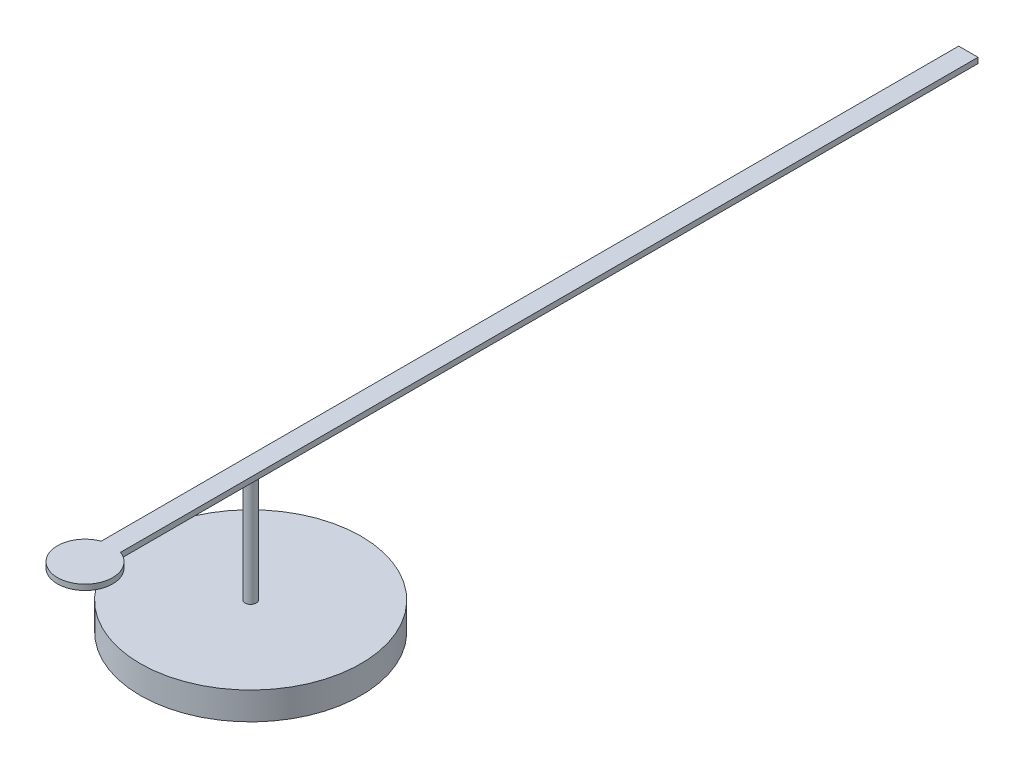
SolidWorks part; units mm, degrees
ref_plane "Front Plane" through (0, 0, 0) normal (0, 0, 1) x (1, 0, 0)
ref_plane "Top Plane" through (0, 0, 0) normal (0, 1, 0) x (1, 0, 0)
ref_plane "Right Plane" through (0, 0, 0) normal (1, 0, 0) x (0, 0, -1)
sketch "Sketch1" plane through (0, 0, 0) normal (0, 1, 0) x (1, 0, 0)
  line L0 (0, 71.7393) -> (0, -94.0328) construction
  line L1 (-2.0666, 0) -> (2.0487, 0) construction
  line L2 (-0.175, 0.4684) -> (-0.175, 13)
  line L4 (-0.175, -2.5316) -> (-0.175, -0.4684)
  line L5 (-0.175, 13) -> (0.175, 13)
  line L6 (0.175, -2.5316) -> (0.175, -0.4684)
  line L7 (0.175, 0.4684) -> (0.175, 13)
  line L8 (0.175, 0.4684) -> (0.175, -0.4684)
  line L9 (-0.175, 0.4684) -> (-0.175, -0.4684)
  arc A0 (0.175, -0.4684) -> (0.175, 0.4684) centre (0, 0) ccw construction
  arc A1 (-0.175, 0.4684) -> (-0.175, -0.4684) centre (0, 0) ccw construction
  arc A2 (-0.175, -2.5316) -> (0.175, -2.5316) centre (0, -3) ccw
  point P13 (0, 13)
  dimension "D1" = 0.5
  dimension "D2" = 0.175
  dimension "D4" = 13
  dimension "D3" = 0.5
  dimension "D5" = 2.5316
extrude "Boss-Extrude1" add sketch "Sketch1" along normal blind 0.1
sketch "Sketch2" plane through (0, 0, 0) normal (0, -1, 0) x (1, 0, 0)
  circle A0 centre (0, 0) radius 0.1
  dimension "D1" = 0.2
extrude "Boss-Extrude2" add sketch "Sketch2" along normal blind 2
sketch "Sketch3" plane through (0, -2, 0) normal (0, -1, 0) x (1, 0, 0)
  circle A0 centre (0, 0) radius 2
  dimension "D1" = 4
extrude "Boss-Extrude3" add sketch "Sketch3" along normal blind 0.5
